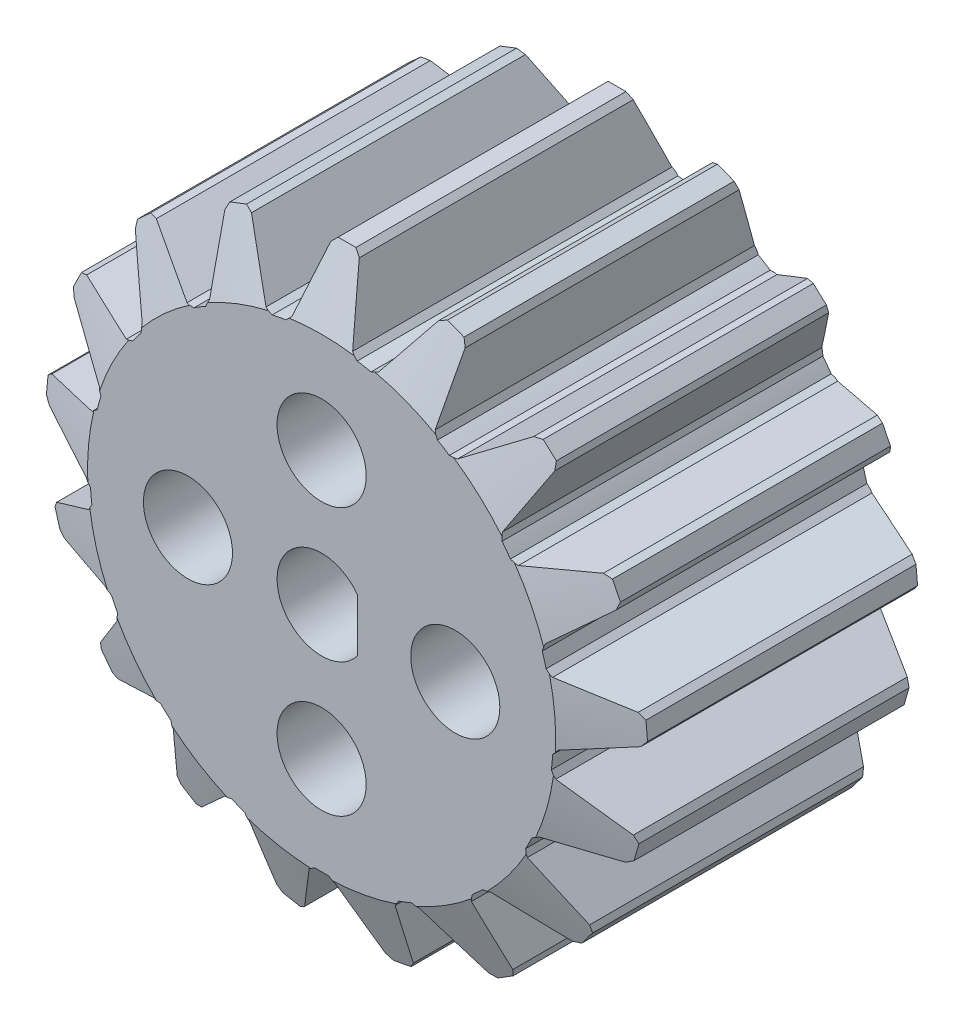
SolidWorks part; units mm, degrees
ref_plane "Front Plane" through (0, 0, 0) normal (0, 0, 1) x (1, 0, 0)
ref_plane "Top Plane" through (0, 0, 0) normal (0, 1, 0) x (1, 0, 0)
ref_plane "Right Plane" through (0, 0, 0) normal (1, 0, 0) x (0, 0, -1)
sketch "Sketch1" plane through (0, 0, 0) normal (0, 0, 1) x (1, 0, 0)
  line L0 (0, 0) -> (0, 16.6022) construction
  circle A0 centre (0, 0) radius 12.99
  circle A2 centre (0, 0) radius 12 construction
  dimension "D1" = 25.98
  dimension "D8" = 24
extrude "Boss-Extrude1" add sketch "Sketch1" along normal blind 18 contours A0
sketch "Sketch2" plane through (0, 0, 18) normal (0, 0, 1) x (1, 0, 0)
  line L0 (0, 0) -> (0, 14.431) construction
  line L1 (-0.8, 16.5926) -> (-1.7, 13.1351)
  line L2 (2, 12.8351) -> (1.7, 13.1351)
  line L3 (-0.8, 16.5926) -> (-0.5, 16.8926)
  line L4 (-2, 12.8351) -> (-1.7, 13.1351)
  line L5 (0.8, 16.5926) -> (1.7, 13.1351)
  line L6 (0.8, 16.5926) -> (0.5, 16.8926)
  line L7 (-2, 12.8351) -> (-2, 12.1173)
  line L8 (2, 12.8351) -> (2, 12.1173)
  line L9 (-2, 12.1173) -> (2, 12.1173)
  arc A1 (0.5, 16.8926) -> (-0.5, 16.8926) centre (0, -74.9815) ccw
  circle A2 centre (0, 0) radius 16.9 construction
  circle A3 centre (0, 0) radius 12.99 construction
  point P1 (-1.5, 12.9031)
  dimension "D7" = 33.8
  dimension "D2" = 4
  dimension "D3" = 1
  dimension "D4" = 1.6
  dimension "D5" = 0.3
  dimension "D6" = 0.3
  dimension "D8" = 0.3
  dimension "D9" = 0.3
  dimension "D10" = 0.3
sketch3d "3DSketch2"
  line L0 (0, 16.894, 18) -> (0, 16.894, -2.0718)
  line L1 (0, 0, 18) -> (0, 14.431, 18) construction
  line L2 (0, 16.894, 18) -> (11.5493, 16.894, 18) construction
  arc A0 (0.5, 16.8926, 18) -> (-0.5, 16.8926, 18) centre (0, -74.9815, 18) ccw construction
  point P5 (0, -74.9815, 109.8754)
  dimension "D1" = 90
sweep "Sweep1" add profiles "Sketch2" path "3DSketch2"
pattern_circular "CirPattern1" count 17 over 360 about axis through (0, 0, 0) along (0, 0, 1) of "Sweep1"
sketch "Sketch4" plane through (0, 0, 18) normal (0, 0, 1) x (1, 0, 0)
  line L0 (-2.5, 0) -> (-2.5, 6.0434) construction
  line L1 (2, 1.5) -> (2, -1.5)
  arc A0 (2, 1.5) -> (2, -1.5) centre (0, 0) ccw
  dimension "D1" = 5
  dimension "D2" = 4.5
extrude "Cut-Extrude1" cut sketch "Sketch4" against normal blind 37
sketch "Sketch5" plane through (0, 0, 0) normal (1, 0, 0) x (0, 0, -1)
  line L0 (0, 0) -> (-28.0609, 0) construction
  line L3 (-22.1801, 9.6373) -> (-22.1801, 25.2002)
  line L4 (-22.1801, 25.2002) -> (5.974, 25.2002)
  line L5 (5.974, 25.2002) -> (5.974, 9.6373)
  line L8 (-1.4271, 16.9099) -> (-16.5729, 16.9099)
  line L9 (0, 13.1351) -> (0, 9.6373)
  line L10 (0, 9.6373) -> (5.974, 9.6373)
  line L12 (-9, 0) -> (-9, 27.6976) construction
  line L13 (-18, -0.4808) -> (-18, 0.7344) construction
  line L14 (-18, 13.1351) -> (-16.5729, 16.9099)
  line L16 (-1.4271, 16.9099) -> (0, 13.1351)
  line L17 (0, 0) -> (0, 21.6134) construction
  line L19 (-18, 13.1351) -> (-18, 9.6373)
  line L21 (-18, 9.6373) -> (-22.1801, 9.6373)
  point P3 (5.974, 9.8916)
  point P17 (0, 0)
  dimension "D2" = 9
revolve "Cut-Revolve1" cut sketch "Sketch5" angle 360 about L0
sketch "Sketch6" plane through (0, 0, 18) normal (0, 0, 1) x (1, 0, 0)
  circle A0 centre (0, 0) radius 7.5 construction
  circle A2 centre (0, 7.5) radius 2.5
  circle A3 centre (7.5, 0) radius 2.5
  circle A4 centre (0, -7.5) radius 2.5
  circle A5 centre (-7.5, 0) radius 2.5
  dimension "D1" = 15
  dimension "D2" = 5
  dimension "D3" = 5
  dimension "D4" = 5
  dimension "D5" = 5
extrude "Cut-Extrude2" cut sketch "Sketch6" against normal blind 37
sketch "Sketch7" plane through (0, 0, 18) normal (0, 0, 1) x (1, 0, 0)
  line L0 (0, 0) -> (0, 31.5274) construction
  line L1 (-2, 12.8351) -> (-2, 18.1794) construction
  line L2 (-0.5, 16.8926) -> (-0.5, 19.6449) construction
  line L3 (-2.5, 11.6247) -> (-2.5, 21.2169) construction
  line L4 (-2.3869, 12.7688) -> (-4.3809, 19.1941) construction
  arc A0 (-2, 12.8351) -> (-2.7716, 12.6909) centre (0, 0) ccw construction
  dimension "D1" = 2
